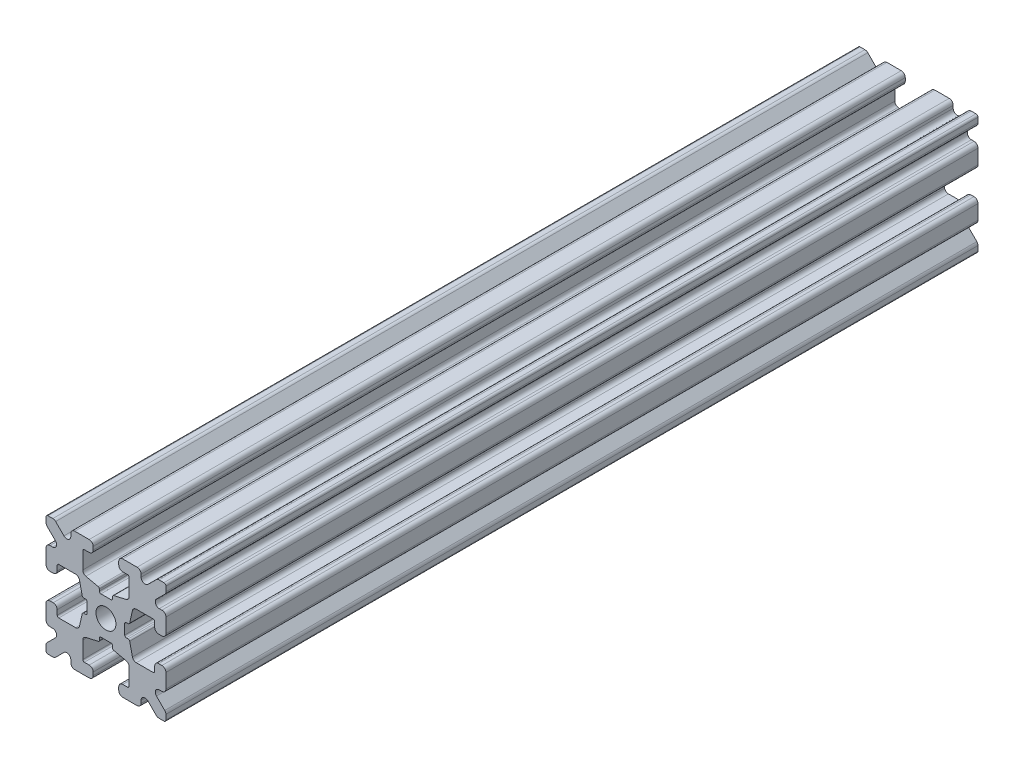
SolidWorks part; units mm, degrees
ref_plane "Front Plane" through (0, 0, 0) normal (0, 0, 1) x (1, 0, 0)
ref_plane "Top Plane" through (0, 0, 0) normal (0, 1, 0) x (1, 0, 0)
ref_plane "Right Plane" through (0, 0, 0) normal (1, 0, 0) x (0, 0, -1)
sketch "Sketch1" plane through (0, 0, 0) normal (0, 0, 1) x (1, 0, 0)
  line L1 (-7.5, -7.5) -> (7.5, -7.5)
  line L2 (-7.5, -7.5) -> (-7.5, 7.5)
  line L3 (-7.5, 7.5) -> (7.5, 7.5)
  line L4 (7.5, -7.5) -> (7.5, 7.5)
  line L5 (-7.5, -7.5) -> (7.5, 7.5) construction
  line L6 (-7.5, 7.5) -> (7.5, -7.5) construction
  circle A0 centre (0, 0) radius 1.25
  point P0 (0, 0)
  dimension "D2" = 2.5
  dimension "D1" = 15
extrude "Boss-Extrude1" add sketch "Sketch1" along normal mid plane 101.6
fillet "Fillet1" radius 0.25 4 edges at (7.5, -7.5, 0) (-7.5, -7.5, 0) (7.5, 7.5, 0) (-7.5, 7.5, 0)
sketch "Sketch2" plane through (0, 0, 50.8) normal (0, 0, 1) x (1, 0, 0)
  line L0 (-7.5, 7.25) -> (-7.5, -7.25) construction
  line L1 (-7.5, 1.6) -> (-6.1, 1.6)
  line L2 (-7.5, 1.6) -> (-7.5, -1.6)
  line L3 (-7.5, -1.6) -> (-6.1, -1.6)
  line L4 (-6.1, 1.6) -> (-6.1, 2.9)
  line L5 (0, 0) -> (-12.1036, 0) construction
  line L6 (-6.1, -2.9) -> (-3.4, -2.9)
  line L7 (0, 0) -> (-7.25, 7.25) construction
  line L8 (-6.1, 2.9) -> (-3.4, 2.9)
  line L9 (-3.4, -2.9) -> (-3.4, 2.9)
  line L10 (55, 0) -> (-55, 0) construction
  line L11 (-6.1, -2.9) -> (-6.1, -1.6)
  line L12 (2.9, 6.1) -> (1.6, 6.1)
  line L13 (2.9, 3.4) -> (-2.9, 3.4)
  line L14 (-2.9, 6.1) -> (-2.9, 3.4)
  line L15 (2.9, 6.1) -> (2.9, 3.4)
  line L16 (-1.6, 6.1) -> (-2.9, 6.1)
  line L17 (1.6, 7.5) -> (1.6, 6.1)
  line L18 (-1.6, 7.5) -> (1.6, 7.5)
  line L19 (-1.6, 7.5) -> (-1.6, 6.1)
  line L20 (-1.6, -7.5) -> (-1.6, -6.1)
  line L21 (-1.6, -7.5) -> (1.6, -7.5)
  line L22 (1.6, -7.5) -> (1.6, -6.1)
  line L23 (-1.6, -6.1) -> (-2.9, -6.1)
  line L24 (2.9, -6.1) -> (2.9, -3.4)
  line L25 (-2.9, -6.1) -> (-2.9, -3.4)
  line L26 (2.9, -3.4) -> (-2.9, -3.4)
  line L27 (2.9, -6.1) -> (1.6, -6.1)
  line L28 (6.1, -2.9) -> (6.1, -1.6)
  line L29 (3.4, -2.9) -> (3.4, 2.9)
  line L30 (6.1, 2.9) -> (3.4, 2.9)
  line L31 (6.1, -2.9) -> (3.4, -2.9)
  line L32 (6.1, 1.6) -> (6.1, 2.9)
  line L33 (7.5, -1.6) -> (6.1, -1.6)
  line L34 (7.5, 1.6) -> (7.5, -1.6)
  line L35 (7.5, 1.6) -> (6.1, 1.6)
  dimension "D1" = 3.2
  dimension "D2" = 5.8
  dimension "D3" = 1.4
  dimension "D4" = 2.7
extrude "Cut-Extrude1" cut sketch "Sketch2" against normal through all
sketch "Sketch4" plane through (0, 0, 50.8) normal (0, 0, 1) x (1, 0, 0)
  line L0 (-3.4, 2.9) -> (-2.75, 0)
  line L1 (55, 0) -> (-55, 0) construction
  line L2 (-2.75, 0) -> (-3.4, -2.9)
  line L3 (-3.4, -2.9) -> (-3.4, 2.9) construction
  line L4 (-3.4, 2.9) -> (-3.4, -2.9)
  line L5 (-2.9, 3.4) -> (0, 2.75)
  line L6 (0, 2.75) -> (2.9, 3.4)
  line L7 (2.9, 3.4) -> (-2.9, 3.4)
  line L8 (3.4, 2.9) -> (2.75, 0)
  line L9 (2.75, 0) -> (3.4, -2.9)
  line L10 (3.4, -2.9) -> (3.4, 2.9)
  line L11 (-2.9, -3.4) -> (0, -2.75)
  line L12 (0, -2.75) -> (2.9, -3.4)
  line L13 (2.9, -3.4) -> (-2.9, -3.4)
  circle A2 centre (0, 0) radius 2.75
  circle A3 centre (0, 0) radius 2.75 construction
  dimension "D1" = 1.5
extrude "Cut-Extrude3" cut sketch "Sketch4" against normal through all
fillet "Fillet3" radius 0.5 16 edges at (-6.1, -1.6, 0) (-7.5, -1.6, 0) (-6.1, 1.6, 0) (-7.5, 1.6, 0) (-1.6, -7.5, 0) (-1.6, -6.1, 0) (1.6, -7.5, 0) (1.6, -6.1, 0) (6.1, -1.6, 0) (7.5, -1.6, 0) (7.5, 1.6, 0) (6.1, 1.6, 0) (1.6, 7.5, 0) (1.6, 6.1, 0) (-1.6, 7.5, 0) (-1.6, 6.1, 0)
fillet "Fillet4" radius 0.5 8 edges at (-3.4, 2.9, 0) (-3.4, -2.9, 0) (2.9, -3.4, 0) (-2.9, -3.4, 0) (3.4, -2.9, 0) (3.4, 2.9, 0) (-2.9, 3.4, 0) (2.9, 3.4, 0)
fillet "Fillet5" radius 3 4 edges at (0, -2.75, 0) (2.75, 0, 0) (-2.75, 0, 0) (0, 2.75, 0)
fillet "Fillet6" radius 0.2 8 edges at (-2.9, -6.1, 0) (2.9, -6.1, 0) (6.1, -2.9, 0) (6.1, 2.9, 0) (2.9, 6.1, 0) (-2.9, 6.1, 0) (-6.1, -2.9, 0) (-6.1, 2.9, 0)
sketch "Sketch5" plane through (0, 0, 50.8) normal (0, 0, 1) x (1, 0, 0)
  line L0 (0, 0) -> (-7.25, 7.25) construction
  line L1 (-7.5, 6.4393) -> (-5.4607, 4.4)
  line L2 (-6.4393, 7.5) -> (-4.4, 5.4607)
  line L3 (-7.5, 4.4) -> (-5.4607, 4.4)
  line L4 (-3.8003, 2.9) -> (-5.9, 2.9) construction
  line L5 (0, 0) -> (-12.1819, 0) construction
  line L6 (-4.4, 7.5) -> (-4.4, 5.4607)
  line L7 (-2.9, 5.9) -> (-2.9, 3.8003) construction
  line L8 (-7.5, 6.4393) -> (-7.5, 4.4)
  line L9 (-7.5, 7.25) -> (-7.5, 2.1) construction
  line L10 (2.1, -7.5) -> (7.25, -7.5) construction
  line L11 (7.5, -7.25) -> (7.5, -2.1) construction
  line L12 (7.25, 7.5) -> (2.1, 7.5) construction
  line L13 (-2.1, 7.5) -> (-7.25, 7.5) construction
  line L14 (-4.4, 7.5) -> (-6.4393, 7.5)
  line L16 (55, 0) -> (-55, 0) construction
  line L17 (0, 0) -> (0, 10.993) construction
  line L18 (0, -54.6431) -> (0, 54.6431) construction
  line L20 (4.4, 7.5) -> (6.4393, 7.5)
  line L22 (7.5, 6.4393) -> (7.5, 4.4)
  line L23 (4.4, 7.5) -> (4.4, 5.4607)
  line L24 (7.5, 4.4) -> (5.4607, 4.4)
  line L25 (6.4393, 7.5) -> (4.4, 5.4607)
  line L26 (7.5, 6.4393) -> (5.4607, 4.4)
  line L27 (7.5, -6.4393) -> (5.4607, -4.4)
  line L28 (6.4393, -7.5) -> (4.4, -5.4607)
  line L29 (7.5, -4.4) -> (5.4607, -4.4)
  line L30 (4.4, -7.5) -> (4.4, -5.4607)
  line L31 (7.5, -6.4393) -> (7.5, -4.4)
  line L33 (4.4, -7.5) -> (6.4393, -7.5)
  line L36 (-4.4, -7.5) -> (-6.4393, -7.5)
  line L38 (-7.5, -6.4393) -> (-7.5, -4.4)
  line L39 (-4.4, -7.5) -> (-4.4, -5.4607)
  line L40 (-7.5, -4.4) -> (-5.4607, -4.4)
  line L41 (-6.4393, -7.5) -> (-4.4, -5.4607)
  line L42 (-7.5, -6.4393) -> (-5.4607, -4.4)
  dimension "D1" = 1.5
  dimension "D2" = 1.5
  dimension "D3" = 1.5
extrude "Cut-Extrude4" cut sketch "Sketch5" against normal through all
fillet "Fillet8" radius 0.5 24 edges at (-5.4607, 4.4, 0) (-7.5, 4.4, 0) (-5.4607, -4.4, 0) (-7.5, -4.4, 0) (-4.4, -7.5, 0) (-4.4, -5.4607, 0) (4.4, -7.5, 0) (4.4, -5.4607, 0) (5.4607, -4.4, 0) (7.5, -4.4, 0) (7.5, 4.4, 0) (5.4607, 4.4, 0) (4.4, 5.4607, 0) (4.4, 7.5, 0) (-4.4, 5.4607, 0) (-4.4, 7.5, 0) (-6.4393, 7.5, 0) (-7.5, 6.4393, 0) (6.4393, 7.5, 0) (7.5, 6.4393, 0) (6.4393, -7.5, 0) (7.5, -6.4393, 0) (-6.4393, -7.5, 0) (-7.5, -6.4393, 0)
sketch "Sketch6" plane through (0, 0, 50.8) normal (0, 0, 1) x (1, 0, 0)
  line L0 (0, 0) -> (0, 11.013) construction
  line L1 (0.6561, 2.8971) -> (2.1235, 2.8971) construction
  line L2 (0, -54.6431) -> (0, 54.6431) construction
  line L3 (0, 0) -> (7.25, 7.25) construction
  line L4 (7.5, 0.8255) -> (7.5, -0.8255)
  line L5 (2.3471, 0.8255) -> (7.5, 0.8255)
  line L6 (0, 0) -> (12.4016, 0) construction
  line L7 (0.8255, -7.5) -> (-0.8255, -7.5)
  line L8 (2.3471, -0.8255) -> (2.3471, 0.8255)
  line L9 (0.8255, -2.3471) -> (0.8255, -7.5)
  line L10 (7.5, -0.8255) -> (2.3471, -0.8255)
  line L11 (-7.5, -0.8255) -> (-2.3471, -0.8255)
  line L12 (-2.3471, -0.8255) -> (-2.3471, 0.8255)
  line L13 (-0.8255, -2.3471) -> (0.8255, -2.3471)
  line L14 (-0.8255, 7.5) -> (-0.8255, 2.3471)
  line L15 (-0.8255, 2.3471) -> (0.8255, 2.3471)
  line L16 (-0.8255, -7.5) -> (-0.8255, -2.3471)
  line L17 (0.8255, 2.3471) -> (0.8255, 7.5)
  line L18 (0.8255, 7.5) -> (-0.8255, 7.5)
  line L19 (3.9, 7.5) -> (2.1, 7.5) construction
  line L20 (-2.3471, 0.8255) -> (-7.5, 0.8255)
  line L21 (-7.5, 0.8255) -> (-7.5, -0.8255)
  point P5 (0, -2.5973)
  point P7 (0, 2.5973)
  dimension "D3" = 0.55
  dimension "D1" = 1.651
extrude "Cut-Extrude5" cut sketch "Sketch6" against normal through all
fillet "Fillet10" radius 0.2 16 edges at (-2.935, 0.8255, 0) (-2.935, -0.8255, 0) (2.935, -0.8255, 0) (2.935, 0.8255, 0) (0.8255, 2.935, 0) (-0.8255, 2.935, 0) (-2.3471, 0.8255, 0) (-2.3471, -0.8255, 0) (0.8255, 2.3471, 0) (-0.8255, 2.3471, 0) (2.3471, 0.8255, 0) (2.3471, -0.8255, 0) (0.8255, -2.935, 0) (0.8255, -2.3471, 0) (-0.8255, -2.3471, 0) (-0.8255, -2.935, 0)
